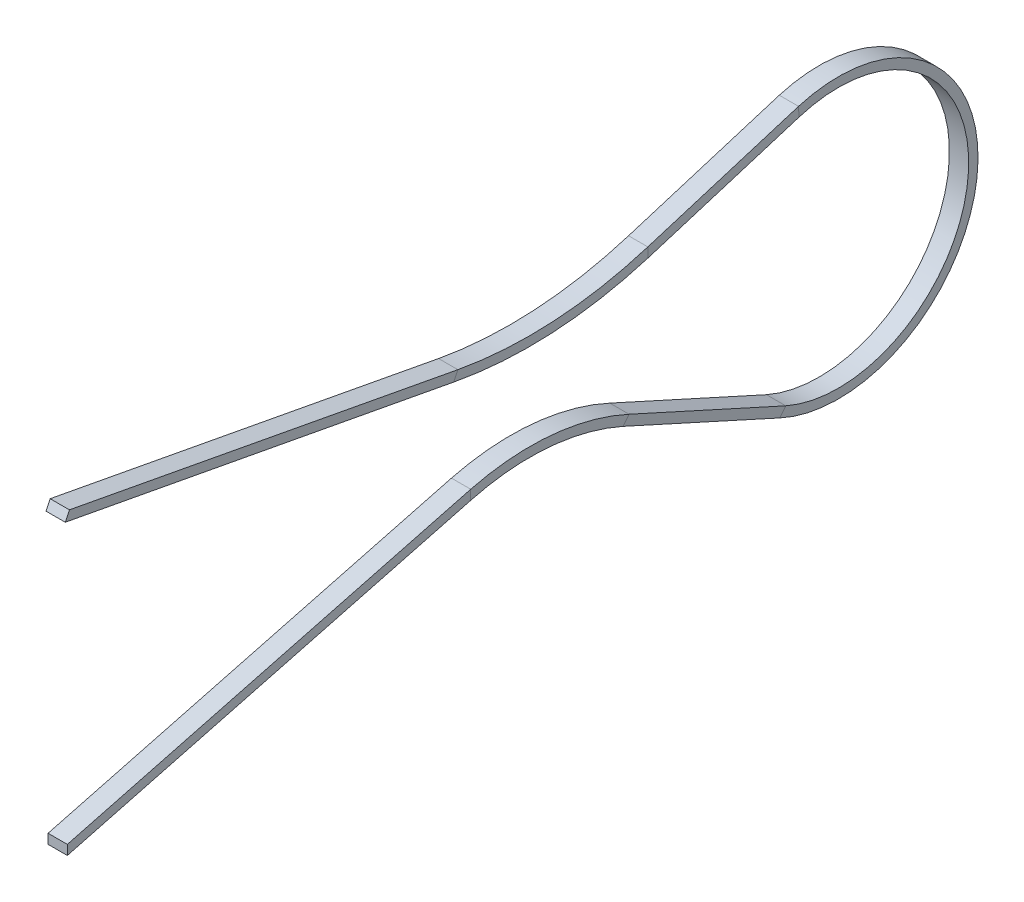
SolidWorks part; units mm, degrees
material "1.0558 (G300)"
ref_plane "Ön Düzlem" through (0, 0, 0) normal (0, 0, 1) x (1, 0, 0)
ref_plane "Üst Düzlem" through (0, 0, 0) normal (0, 1, 0) x (1, 0, 0)
ref_plane "Sağ Düzlem" through (0, 0, 0) normal (1, 0, 0) x (0, 0, -1)
sketch "Çizim1" plane through (0, 0, 0) normal (0, 0, 1) x (1, 0, 0)
  line L1 (-0.5, 0.25) -> (0.5, 0.25)
  line L2 (-0.5, 0.25) -> (-0.5, -0.25)
  line L3 (-0.5, -0.25) -> (0.5, -0.25)
  line L4 (0.5, 0.25) -> (0.5, -0.25)
  line L5 (-0.5, 0.25) -> (0.5, -0.25) construction
  line L6 (-0.5, -0.25) -> (0.5, 0.25) construction
  point P0 (0, 0)
  dimension "D1" = 1
  dimension "D2" = 0.5
sketch "Çizim2" plane through (0, 0, 0) normal (1, 0, 0) x (0, 0, -1)
  line L8 (0, 0) -> (20.9254, 5.4919)
  line L10 (37.9422, 14.1907) -> (30.1236, 11.786)
  line L13 (28.9851, 4.8089) -> (37.109, 1.1249)
  line L14 (20.1506, 11.2218) -> (0, 15)
  arc A3 (37.109, 1.1249) -> (37.9422, 14.1907) centre (40, 7.5) ccw
  arc A4 (20.1506, 11.2218) -> (30.1236, 11.786) centre (23.9935, 31.7172) ccw
  arc A5 (20.9254, 5.4919) -> (28.9851, 4.8089) centre (23.9935, -6.1983) cw
  dimension "D2" = 7
  dimension "D1" = 40
  dimension "D3" = 15
  dimension "D4" = 7.5
sweep "Süpür1" add profiles "Çizim1" path "Çizim2"
